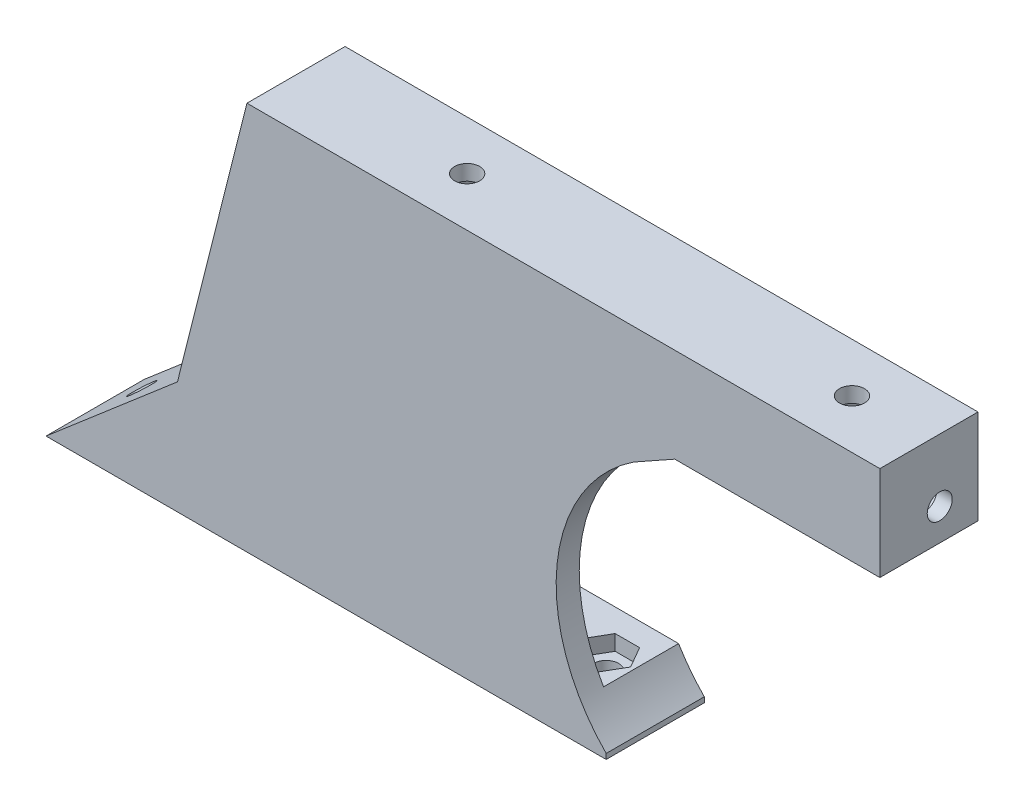
SolidWorks part; units mm, degrees
ref_plane "Alzado" through (0, 0, 0) normal (0, 0, 1) x (1, 0, 0)
ref_plane "Planta" through (0, 0, 0) normal (0, 1, 0) x (1, 0, 0)
ref_plane "Vista lateral" through (0, 0, 0) normal (1, 0, 0) x (0, 0, -1)
sketch "Croquis1" plane through (0, 0, 0) normal (0, 0, 1) x (1, 0, 0)
  line L3 (-46.6759, 50.5119) -> (-55.7, 14.6421)
  line L5 (-72.7832, 0) -> (-32.9594, 34.1331) construction
  line L6 (-55.7, 14.6421) -> (-72.7832, 0)
  line L7 (-72.7832, 0) -> (0, 0)
  line L8 (0, 0) -> (0, 0.6807)
  line L9 (8.9133, 38.25) -> (3.5627, 35.25)
  line L10 (8.9133, 38.25) -> (35.5627, 38.25)
  line L11 (35.5627, 38.25) -> (35.5627, 50.5119)
  line L12 (-46.6759, 50.5119) -> (35.5627, 50.5119)
  arc A0 (3.5627, 35.25) -> (0, 0.6807) centre (16, 16.5) ccw
  dimension "D1" = 22.5
  dimension "D2" = 46.6759
  dimension "D3" = 55.7
extrude "Saliente-Extruir1" add sketch "Croquis1" against normal blind 3
sketch "Croquis2" plane through (0, 0, -3) normal (0, 0, -1) x (-1, 0, 0)
  line L0 (42.5264, 46.5119) -> (51.239, 11.8804)
  line L2 (-35.5627, 38.25) -> (-35.5627, 50.5119) construction
  line L3 (-35.5627, 50.5119) -> (46.6759, 50.5119) construction
  line L4 (-8.9133, 38.25) -> (-35.5627, 38.25) construction
  line L6 (-35.5627, 50.5119) -> (-35.5627, 38.25)
  line L7 (-35.5627, 38.25) -> (-31.5627, 38.25)
  line L9 (-31.5627, 50.5119) -> (-31.5627, 46.5119) construction
  line L10 (-31.5627, 38.25) -> (-31.5627, 46.5119)
  line L11 (-31.5627, 46.5119) -> (42.5264, 46.5119)
  line L12 (-35.5627, 50.5119) -> (46.6759, 50.5119)
  line L13 (46.6759, 50.5119) -> (55.7, 14.6421)
  line L14 (55.7, 14.6421) -> (72.7832, 0)
  line L15 (72.7832, 0) -> (0, 0)
  line L16 (0, 0) -> (0, 0.6807)
  line L17 (36.3916, 0) -> (36.3916, 5) construction
  line L18 (3.3391, 5) -> (59.2664, 5)
  line L21 (51.239, 11.8804) -> (59.2664, 5)
  arc A0 (0, 0.6807) -> (-3.5627, 35.25) centre (-16, 16.5) ccw construction
  arc A1 (0, 0.6807) -> (3.3391, 5) centre (-16, 16.5) ccw
  dimension "D1" = 4
  dimension "D2" = 38.9017
  dimension "D3" = 78.0891
  dimension "D4" = 86.8016
  dimension "D5" = 94.8291
  dimension "D6" = 38.6316
extrude "Saliente-Extruir2" add sketch "Croquis2" along normal blind 9.75
sketch "Croquis4" plane through (0, 0, 0) normal (0, -1, 0) x (1, 0, 0)
  circle A0 centre (-7, -7) radius 1.625
  circle A1 centre (-52.7832, -7) radius 1.625
  dimension "D1" = 3.25
extrude "Cortar-Extruir1" cut sketch "Croquis4" against normal up to vertex (5 mm away)
sketch "Croquis5" plane through (0, 5, 0) normal (0, 1, 0) x (1, 0, 0)
  line L1 (-10.18, 7) -> (-8.59, 4.246)
  line L2 (-8.59, 4.246) -> (-5.41, 4.246)
  line L3 (-5.41, 4.246) -> (-3.82, 7)
  line L4 (-3.82, 7) -> (-5.41, 9.754)
  line L5 (-5.41, 9.754) -> (-8.59, 9.754)
  line L6 (-8.59, 9.754) -> (-10.18, 7)
  line L7 (-49.6032, 7) -> (-51.1932, 9.754)
  line L8 (-51.1932, 9.754) -> (-54.3732, 9.754)
  line L9 (-54.3732, 9.754) -> (-55.9632, 7)
  line L10 (-55.9632, 7) -> (-54.3732, 4.246)
  line L11 (-54.3732, 4.246) -> (-51.1932, 4.246)
  line L12 (-51.1932, 4.246) -> (-49.6032, 7)
  circle A0 centre (-7, 7) radius 2.754 construction
  circle A1 centre (-52.7832, 7) radius 2.754 construction
  dimension "D1" = 5.5079
extrude "Cortar-Extruir2" cut sketch "Croquis5" against normal blind 2
sketch "Croquis6" plane through (-30.8242, 35.9632, 0) normal (-0.6508, 0.7593, 0) x (0.7593, 0.6508, 0)
  line L1 (-55.2622, 6.375) -> (-32.7627, 6.375) construction
  line L2 (-55.2622, 12.75) -> (-55.2622, 0) construction
  line L3 (-32.7627, 12.75) -> (-32.7627, 0) construction
  line L4 (-47.2622, 0) -> (-47.2622, 12.75) construction
  line L5 (-55.2622, 12.75) -> (-32.7627, 12.75) construction
  circle A0 centre (-47.2622, 6.375) radius 1.625
  dimension "D1" = 3.25
extrude "Cortar-Extruir3" cut sketch "Croquis6" against normal blind 9
sketch "Croquis9" plane through (-30.8242, 35.9632, 0) normal (-0.6508, 0.7593, 0) x (0.7593, 0.6508, 0)
  line L1 (-50.4322, 6.375) -> (-48.8472, 3.6297)
  line L2 (-48.8472, 3.6297) -> (-45.6772, 3.6297)
  line L3 (-45.6772, 3.6297) -> (-44.0922, 6.375)
  line L4 (-44.0922, 6.375) -> (-45.6772, 9.1203)
  line L5 (-45.6772, 9.1203) -> (-48.8472, 9.1203)
  line L6 (-48.8472, 9.1203) -> (-50.4322, 6.375)
  circle A0 centre (-47.2622, 6.375) radius 2.7453 construction
  dimension "D1" = 5.4906
extrude "Cortar-Extruir4" cut sketch "Croquis9" against normal blind 10
sketch "Croquis10" plane through (-30.8242, 35.9632, 0) normal (-0.6508, 0.7593, 0) x (0.7593, 0.6508, 0)
  line L0 (-50.4322, 6.375) -> (-44.0922, 6.375) construction
  line L1 (-47.2622, 3.6297) -> (-47.2622, 9.1203) construction
  line L2 (-48.8472, 3.6297) -> (-45.6772, 3.6297) construction
  line L3 (-45.6772, 9.1203) -> (-48.8472, 9.1203) construction
  line L5 (-50.4322, 6.375) -> (-48.8472, 3.6297)
  line L6 (-48.8472, 3.6297) -> (-45.6772, 3.6297)
  line L7 (-45.6772, 3.6297) -> (-44.0922, 6.375)
  line L8 (-44.0922, 6.375) -> (-45.6772, 9.1203)
  line L9 (-45.6772, 9.1203) -> (-48.8472, 9.1203)
  line L10 (-48.8472, 9.1203) -> (-50.4322, 6.375)
  circle A0 centre (-47.2622, 6.375) radius 1.625
  circle A1 centre (-47.2622, 6.375) radius 2.7453 construction
  dimension "D1" = 3.25
extrude "Saliente-Extruir3" add sketch "Croquis10" against normal blind 2
sketch "Croquis13" plane through (-55.8489, 14.0503, 0) normal (-0.9698, 0.244, 0) x (0, 0, 1)
  line L0 (-6.375, 19.104) -> (-6.375, 28.3508) construction
  line L1 (-6.375, 28.3508) -> (-6.375, 37.5977) construction
  line L2 (-12.75, 37.5977) -> (0, 37.5977) construction
  line L4 (-6.375, 20.5474) -> (-3.621, 22.1374)
  line L5 (-3.621, 22.1374) -> (-3.621, 25.3174)
  line L6 (-3.621, 25.3174) -> (-6.375, 26.9074)
  line L7 (-6.375, 26.9074) -> (-9.129, 25.3174)
  line L8 (-9.129, 25.3174) -> (-9.129, 22.1374)
  line L9 (-9.129, 22.1374) -> (-6.375, 20.5474)
  circle A2 centre (-6.375, 23.7274) radius 2.754 construction
  dimension "D1" = 10.6903
  dimension "D2" = 5.5079
extrude "Cortar-Extruir5" cut sketch "Croquis13" against normal up to vertex (5 mm away)
sketch "Croquis14" plane through (-55.8489, 14.0503, 0) normal (-0.9698, 0.244, 0) x (0, 0, 1)
  line L0 (-6.375, 26.9074) -> (-6.375, 20.5474) construction
  line L2 (-6.375, 26.9074) -> (-9.129, 25.3174)
  line L3 (-9.129, 25.3174) -> (-9.129, 22.1374)
  line L4 (-9.129, 22.1374) -> (-6.375, 20.5474)
  line L5 (-6.375, 20.5474) -> (-3.621, 22.1374)
  line L6 (-3.621, 22.1374) -> (-3.621, 25.3174)
  line L7 (-3.621, 25.3174) -> (-6.375, 26.9074)
  circle A0 centre (-6.375, 23.7274) radius 2.754 construction
  circle A1 centre (-6.375, 23.7274) radius 1.625
  dimension "D1" = 3.25
extrude "Saliente-Extruir4" add sketch "Croquis14" against normal blind 3
sketch "Croquis15" plane through (0, 50.5119, 0) normal (0, 1, 0) x (1, 0, 0)
  line L2 (35.5627, 0) -> (-46.6759, 0) construction
  line L4 (35.5627, 12.75) -> (35.5627, 0) construction
  circle A2 centre (25.5627, 6.375) radius 1.625
  circle A3 centre (-24.4373, 6.375) radius 1.625
  dimension "D1" = 3.25
  dimension "D2" = 10
  dimension "D3" = 60
  dimension "D4" = 6.375
extrude "Cortar-Extruir6" cut sketch "Croquis15" against normal up to vertex (4 mm away)
sketch "Croquis16" plane through (0, 46.5119, 0) normal (0, -1, 0) x (1, 0, 0)
  line L1 (22.3827, -6.375) -> (23.9727, -9.129)
  line L2 (23.9727, -9.129) -> (27.1527, -9.129)
  line L3 (27.1527, -9.129) -> (28.7427, -6.375)
  line L4 (28.7427, -6.375) -> (27.1527, -3.621)
  line L5 (27.1527, -3.621) -> (23.9727, -3.621)
  line L6 (23.9727, -3.621) -> (22.3827, -6.375)
  line L7 (-21.2573, -6.375) -> (-22.8473, -3.621)
  line L8 (-22.8473, -3.621) -> (-26.0273, -3.621)
  line L9 (-26.0273, -3.621) -> (-27.6173, -6.375)
  line L10 (-27.6173, -6.375) -> (-26.0273, -9.129)
  line L11 (-26.0273, -9.129) -> (-22.8473, -9.129)
  line L12 (-22.8473, -9.129) -> (-21.2573, -6.375)
  circle A0 centre (25.5627, -6.375) radius 2.754 construction
  circle A1 centre (-24.4373, -6.375) radius 2.754 construction
  dimension "D1" = 5.5079
extrude "Cortar-Extruir7" cut sketch "Croquis16" against normal blind 2
sketch "Croquis17" plane through (35.5627, 0, 0) normal (1, 0, 0) x (0, 0, -1)
  circle A0 centre (7.7775, 42.38) radius 1.625
  dimension "D1" = 3.25
extrude "Cortar-Extruir9" cut sketch "Croquis17" against normal up to vertex (4 mm away)
sketch "Croquis18" plane through (31.5627, 0, 0) normal (-1, 0, 0) x (0, 0, 1)
  line L1 (-7.7775, 39.2) -> (-5.0235, 40.79)
  line L2 (-5.0235, 40.79) -> (-5.0235, 43.97)
  line L3 (-5.0235, 43.97) -> (-7.7775, 45.56)
  line L4 (-7.7775, 45.56) -> (-10.5315, 43.97)
  line L5 (-10.5315, 43.97) -> (-10.5315, 40.79)
  line L6 (-10.5315, 40.79) -> (-7.7775, 39.2)
  circle A0 centre (-7.7775, 42.38) radius 2.754 construction
  dimension "D1" = 5.5079
extrude "Cortar-Extruir10" cut sketch "Croquis18" against normal blind 2
